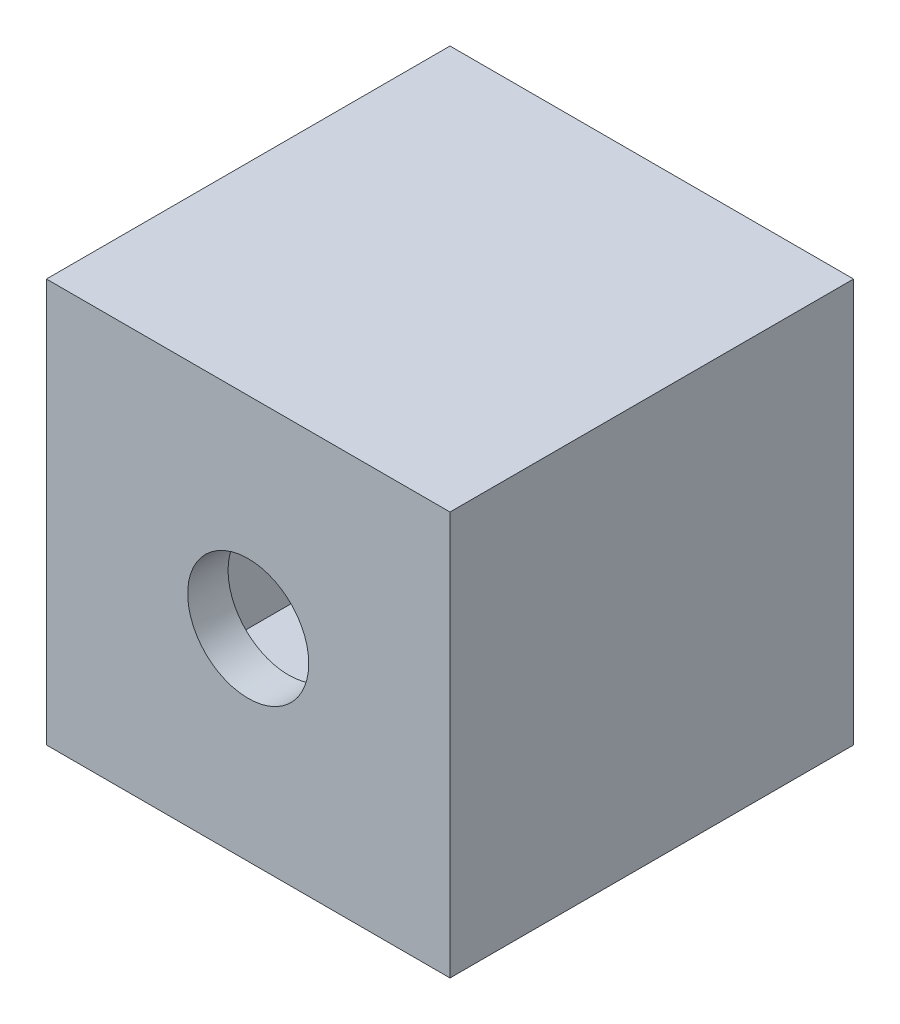
SolidWorks part; units mm, degrees
material "Beech"
ref_plane "Front Plane" through (0, 0, 0) normal (0, 0, 1) x (1, 0, 0)
ref_plane "Top Plane" through (0, 0, 0) normal (0, 1, 0) x (1, 0, 0)
ref_plane "Right Plane" through (0, 0, 0) normal (1, 0, 0) x (0, 0, -1)
sketch "Sketch5" plane through (0, 0, 0) normal (0, 0, 1) x (1, 0, 0)
  line L1 (-100, -100) -> (100, -100)
  line L2 (-100, -100) -> (-100, 100)
  line L3 (-100, 100) -> (100, 100)
  line L4 (100, -100) -> (100, 100)
  line L5 (-100, -100) -> (100, 100) construction
  line L6 (-100, 100) -> (100, -100) construction
  point P0 (0, 0)
  dimension "D1" = 200
  dimension "D2" = 200
extrude "Boss-Extrude2" add sketch "Sketch5" along normal blind 200
shell "Shell2" thickness 20
sketch "Sketch6" plane through (0, 0, 200) normal (0, 0, 1) x (1, 0, 0)
  circle A0 centre (0, 0) radius 30
  dimension "D1" = 60
extrude "Cut-Extrude2" cut sketch "Sketch6" against normal blind 51.6
